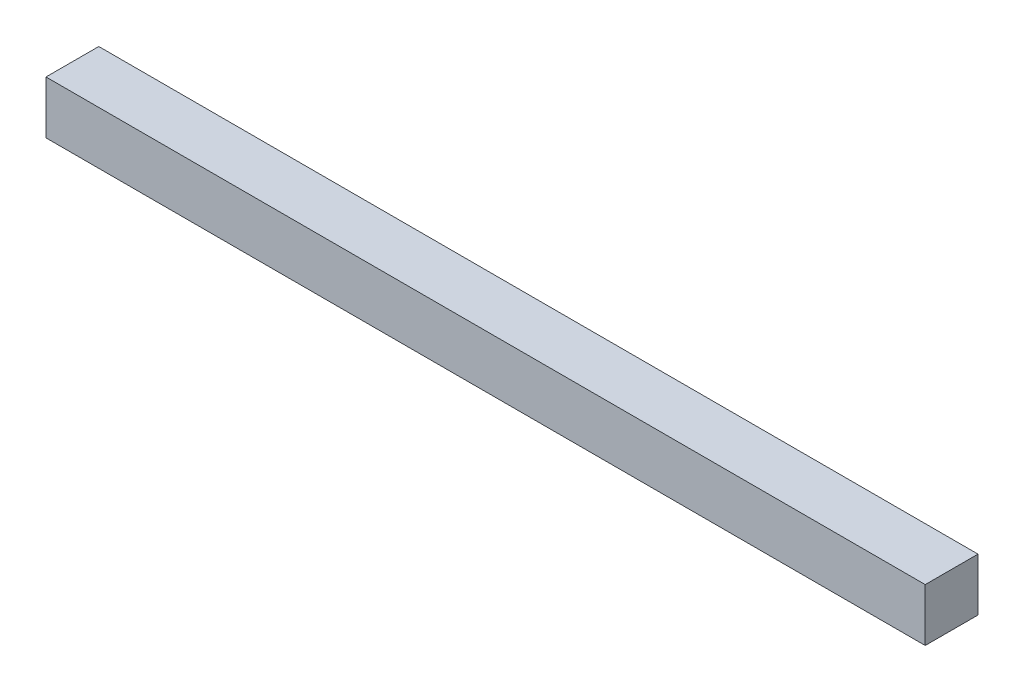
SolidWorks part; units mm, degrees
material "AISI 304"
ref_plane "Front Plane" through (0, 0, 0) normal (0, 0, 1) x (1, 0, 0)
ref_plane "Top Plane" through (0, 0, 0) normal (0, 1, 0) x (1, 0, 0)
ref_plane "Right Plane" through (0, 0, 0) normal (1, 0, 0) x (0, 0, -1)
sketch "Sketch1" plane through (0, 0, 0) normal (1, 0, 0) x (0, 0, -1)
  line L1 (0, 0) -> (25.4, 0)
  line L2 (0, 0) -> (0, 25.4)
  line L3 (0, 25.4) -> (25.4, 25.4)
  line L4 (25.4, 0) -> (25.4, 25.4)
  dimension "D1" = 25.4
  dimension "D2" = 25.4
extrude "Boss-Extrude1" add sketch "Sketch1" along normal blind 423.164
